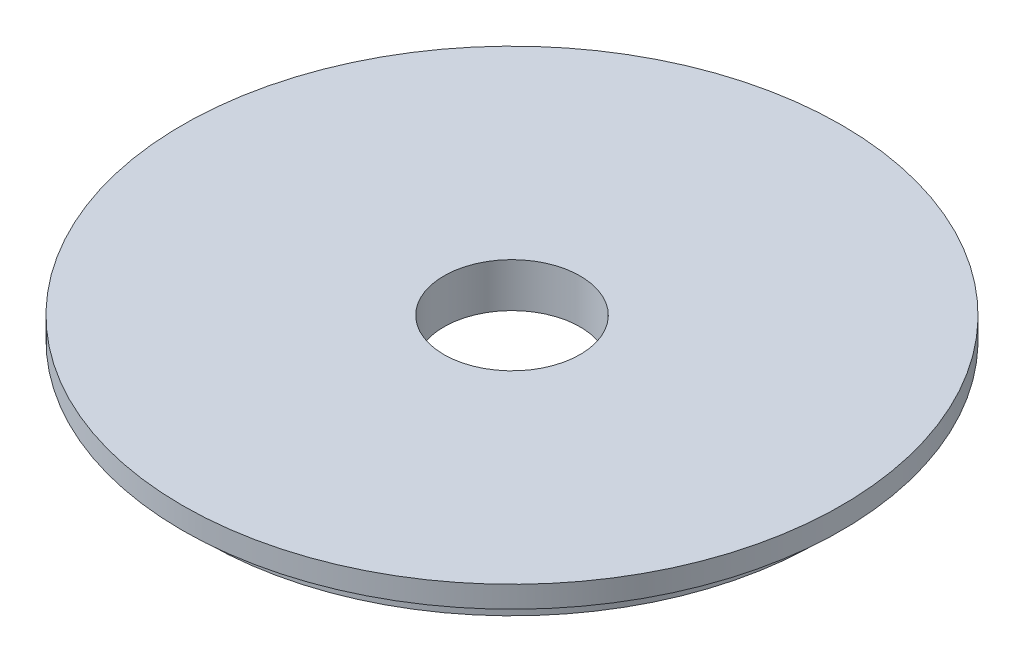
SolidWorks part; units mm, degrees
material "Phenolic Fiber Filled"
ref_plane "Front Plane" through (0, 0, 0) normal (0, 0, 1) x (1, 0, 0)
ref_plane "Top Plane" through (0, 0, 0) normal (0, 1, 0) x (1, 0, 0)
ref_plane "Right Plane" through (0, 0, 0) normal (1, 0, 0) x (0, 0, -1)
sketch "Sketch1" plane through (0, 0, 0) normal (0, 0, 1) x (1, 0, 0)
  line L0 (0, 0) -> (-9.525, 0) construction
  line L1 (-9.525, 0) -> (-46.0756, 0)
  line L2 (-46.0756, 0) -> (-46.0756, -3.0226)
  line L3 (-46.0756, -3.0226) -> (-42.7482, -3.0226)
  line L4 (-42.7482, -3.0226) -> (-42.7482, -6.1722)
  line L5 (-42.7482, -6.1722) -> (-9.525, -6.1722)
  line L6 (-9.525, -6.1722) -> (-9.525, 0)
  line L7 (0, 0) -> (0, -5.0066) construction
  dimension "D1" = 9.525
  dimension "D2" = 46.0756
  dimension "D3" = 42.7482
  dimension "D4" = 6.1722
  dimension "D5" = 3.0226
revolve "Revolve1" add sketch "Sketch1" angle 360 about L7
